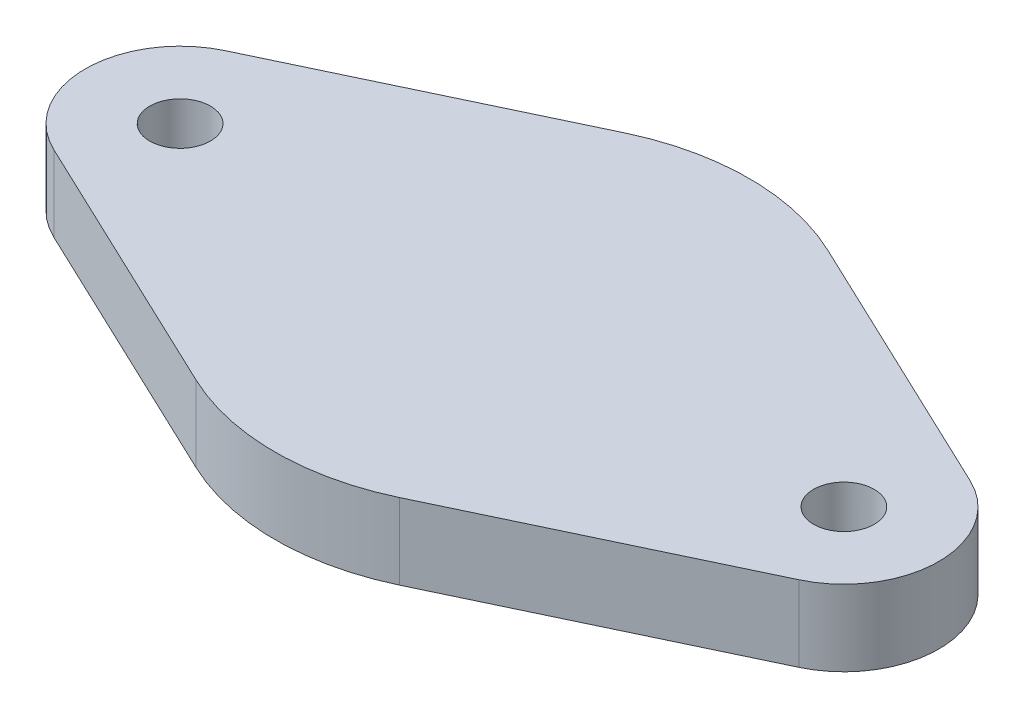
SolidWorks part; units mm, degrees
ref_plane "Front Plane" through (0, 0, 0) normal (0, 0, 1) x (1, 0, 0)
ref_plane "Top Plane" through (0, 0, 0) normal (0, 1, 0) x (1, 0, 0)
ref_plane "Right Plane" through (0, 0, 0) normal (1, 0, 0) x (0, 0, -1)
ref_axis "Axis1" through (0, 12.495, 0) along (0, -1, 0)
sketch "Sketch1" plane through (0, 0, 0) normal (0, 0, 1) x (1, 0, 0)
  line L5 (12.5, 7.9) -> (0, 0) construction
  line L6 (0, 0) -> (-12.5, 7.9) construction
  line L7 (6.5309, 7.9) -> (12.5, 7.9)
  line L10 (0, 11.9) -> (12.5, 11.9)
  line L11 (12.5, 7.9) -> (12.5, 11.9)
  line L12 (6.5309, 7.9) -> (12.5, 7.9)
  line L13 (0, 10.25) -> (0, 11.9)
  arc A0 (6.5309, 7.9) -> (0, 10.25) centre (0, 0) ccw
  dimension "D1" = 20.5
  dimension "D3" = 25
  dimension "D4" = 4
revolve "Revolve2" add sketch "Sketch1" angle 360 about axis through (0, 12.495, 0) along (0, -1, 0)
sketch "Sketch2" plane through (0, 11.9, 0) normal (0, 1, 0) x (1, 0, 0)
  line L0 (-5.3571, 11.2938) -> (-19.6429, 4.5175)
  line L1 (-31.5087, 0) -> (29.0808, 0) construction
  line L2 (-12.5, 0) -> (-12.5, -6.5741) construction
  line L5 (-5.3571, -11.2938) -> (-19.6429, -4.5175)
  line L7 (5.3571, -11.2938) -> (19.6429, -4.5175)
  line L8 (5.3571, 11.2938) -> (19.6429, 4.5175)
  arc A1 (-19.6429, 4.5175) -> (-19.6429, -4.5175) centre (-17.5, 0) ccw
  arc A2 (19.6429, 4.5175) -> (19.6429, -4.5175) centre (17.5, 0) cw
  arc A3 (-5.3571, 11.2938) -> (-5.3571, -11.2938) centre (0, 0) ccw
  arc A4 (5.3571, -11.2938) -> (5.3571, 11.2938) centre (0, 0) ccw
  circle A5 centre (-17.5, 0) radius 1.6
  circle A6 centre (17.5, 0) radius 1.6
  dimension "D1" = 3.2
  dimension "D2" = 5
extrude "Boss-Extrude1" add sketch "Sketch2" against normal up to surface (4 mm away) up to face at (0, 7.9, 12.5)
